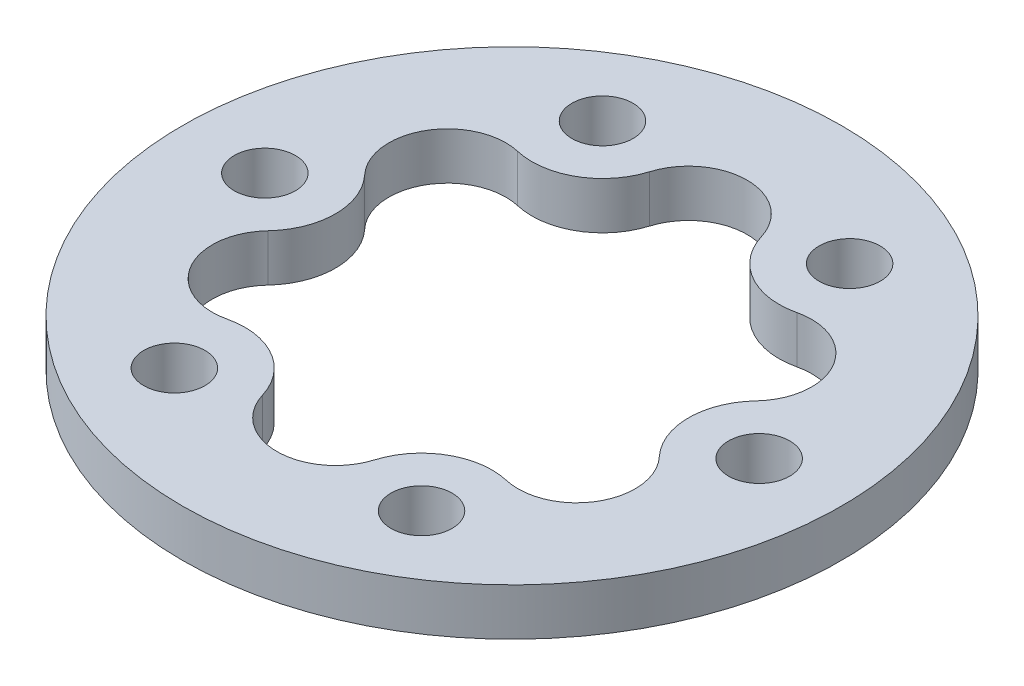
SolidWorks part; units mm, degrees
material "Hexcel AS4C (3000 丝)"
ref_plane "前视基准面" through (0, 0, 0) normal (0, 0, 1) x (1, 0, 0)
ref_plane "上视基准面" through (0, 0, 0) normal (0, 1, 0) x (1, 0, 0)
ref_plane "右视基准面" through (0, 0, 0) normal (1, 0, 0) x (0, 0, -1)
sketch "草图1" plane through (0, 0, 0) normal (0, 1, 0) x (1, 0, 0)
  line L0 (0, 25) -> (0, 0) construction
  line L1 (0, 0) -> (10.5, 18.1865) construction
  circle A0 centre (0, 0) radius 28
  circle A1 centre (0, 0) radius 25 construction
  circle A2 centre (0, 25) radius 1.25 construction
  circle A3 centre (21.6506, 12.5) radius 1.25 construction
  circle A4 centre (21.6506, -12.5) radius 1.25 construction
  circle A5 centre (0, -25) radius 1.25 construction
  circle A6 centre (-21.6506, -12.5) radius 1.25 construction
  circle A7 centre (-21.6506, 12.5) radius 1.25 construction
  circle A8 centre (0, 0) radius 15 construction
  circle A9 centre (0, 15) radius 4 construction
  circle A10 centre (12.9904, -7.5) radius 4 construction
  circle A11 centre (-12.9904, -7.5) radius 4 construction
  circle A12 centre (0, 0) radius 21 construction
  circle A13 centre (10.5, 18.1865) radius 2.6
  circle A14 centre (21, 0) radius 2.6
  circle A15 centre (10.5, -18.1865) radius 2.6
  circle A16 centre (-10.5, -18.1865) radius 2.6
  circle A17 centre (-21, 0) radius 2.6
  circle A18 centre (-10.5, 18.1865) radius 2.6
  dimension "D1" = 2.5
  dimension "D2" = 50
  dimension "D3" = 56
  dimension "D5" = 30
  dimension "D6" = 8
  dimension "D9" = 5.2
  dimension "D10" = 42
  dimension "D8" = 30
  dimension "D4" = 6
  dimension "D7" = 3
  dimension "D11" = 6
extrude "凸台-拉伸1" add sketch "草图1" along normal blind 4
sketch "草图4" plane through (0, 4, 0) normal (0, 1, 0) x (1, 0, 0)
  circle A0 centre (0, 0) radius 15 construction
  circle A1 centre (0, 15) radius 4 construction
  circle A2 centre (12.9904, 7.5) radius 4 construction
  circle A3 centre (12.9904, -7.5) radius 4 construction
  circle A4 centre (0, -15) radius 4 construction
  circle A5 centre (-12.9904, -7.5) radius 4 construction
  circle A6 centre (-12.9904, 7.5) radius 4 construction
  arc A7 (4.7586, 16.4441) -> (11.8617, 12.3431) centre (10.5, 18.1865) ccw
  arc A8 (-4.7586, 16.4441) -> (4.7586, 16.4441) centre (0, 15) cw
  arc A9 (11.8617, 12.3431) -> (16.6203, 4.101) centre (12.9904, 7.5) cw
  arc A10 (16.6203, 4.101) -> (16.6203, -4.101) centre (21, 0) ccw
  arc A11 (16.6203, -4.101) -> (11.8617, -12.3431) centre (12.9904, -7.5) cw
  arc A12 (11.8617, -12.3431) -> (4.7586, -16.4441) centre (10.5, -18.1865) ccw
  arc A13 (4.7586, -16.4441) -> (-4.7586, -16.4441) centre (0, -15) cw
  arc A14 (-4.7586, -16.4441) -> (-11.8617, -12.3431) centre (-10.5, -18.1865) ccw
  arc A15 (-11.8617, -12.3431) -> (-16.6203, -4.101) centre (-12.9904, -7.5) cw
  arc A16 (-16.6203, -4.101) -> (-16.6203, 4.101) centre (-21, 0) ccw
  arc A17 (-16.6203, 4.101) -> (-11.8617, 12.3431) centre (-12.9904, 7.5) cw
  arc A18 (-11.8617, 12.3431) -> (-4.7586, 16.4441) centre (-10.5, 18.1865) ccw
  dimension "D1" = 30
  dimension "D2" = 8
  dimension "D4" = 6
  dimension "D3" = 6
  dimension "D5" = 6
extrude "切除-拉伸2" cut sketch "草图4" against normal through all and the other way through all
move or copy body "实体-移动/复制1" [suppressed] bodies to move or copy 109
